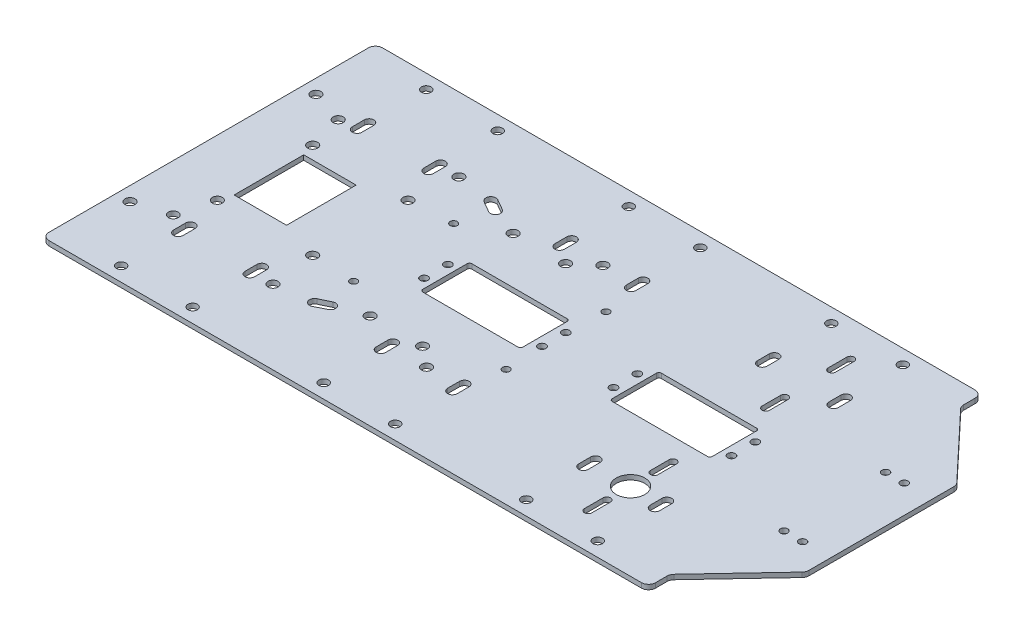
SolidWorks part; units mm, degrees
ref_plane "前视基准面" through (0, 0, 0) normal (0, 0, 1) x (1, 0, 0)
ref_plane "上视基准面" through (0, 0, 0) normal (0, 1, 0) x (1, 0, 0)
ref_plane "右视基准面" through (0, 0, 0) normal (1, 0, 0) x (0, 0, -1)
sketch "草图1" plane through (0, 0, 0) normal (0, 1, 0) x (1, 0, 0)
  line L0 (4082.7289, 1509.8503) -> (4060.7289, 1509.8503)
  line L1 (4175.7346, 1460.2503) -> (4175.7346, 1455.2395)
  line L2 (4145.7346, 1460.2503) -> (4145.7346, 1455.2395)
  line L3 (4179.7346, 1455.2395) -> (4179.7346, 1460.2503)
  line L4 (4115.6347, 1530.6257) -> (4120.1638, 1528.0129)
  line L5 (4060.7289, 1480.6503) -> (4082.7289, 1480.6503)
  line L6 (4094.7346, 1455.2395) -> (4094.7346, 1460.2503)
  line L7 (4149.7346, 1455.2395) -> (4149.7346, 1460.2503)
  line L8 (4122.2625, 1531.6509) -> (4117.7334, 1534.2637)
  line L9 (4060.7346, 1460.2503) -> (4060.7346, 1455.2395)
  line L10 (4234.7346, 1455.2395) -> (4234.7346, 1460.2503)
  line L11 (4064.7346, 1455.2395) -> (4064.7346, 1460.2503)
  line L12 (4090.7346, 1460.2503) -> (4090.7346, 1455.2395)
  line L13 (4060.7289, 1509.8503) -> (4060.7289, 1480.6503)
  line L14 (4082.7289, 1480.6503) -> (4082.7289, 1509.8503)
  line L15 (4090.7346, 1530.2503) -> (4090.7346, 1535.2611)
  line L16 (4176.5776, 1504.5503) -> (4176.5776, 1485.9503)
  line L17 (4175.5776, 1484.9503) -> (4135.5776, 1484.9503)
  line L18 (4094.7346, 1535.2611) -> (4094.7346, 1530.2503)
  line L19 (4115.7772, 1460.3388) -> (4120.3279, 1462.5177)
  line L20 (4149.7346, 1535.2611) -> (4149.7346, 1530.2503)
  line L21 (4060.7346, 1530.2503) -> (4060.7346, 1535.2611)
  line L22 (4145.7346, 1530.2503) -> (4145.7346, 1535.2611)
  line L23 (4122.1349, 1458.8376) -> (4117.6283, 1456.569)
  line L24 (4134.5776, 1485.9503) -> (4134.5776, 1504.5503)
  line L25 (4135.5776, 1505.5503) -> (4175.5776, 1505.5503)
  line L26 (4064.7346, 1535.2611) -> (4064.7346, 1530.2503)
  line L27 (4175.7346, 1530.2503) -> (4175.7346, 1535.2611)
  line L28 (4038.4346, 1425.2395) -> (4287.0345, 1425.2395)
  line L29 (4317.7347, 1464.8467) -> (4317.7347, 1525.6539)
  line L30 (4251.291, 1514.7632) -> (4251.291, 1522.5539)
  line L31 (4251.291, 1542.4908) -> (4251.291, 1550.2815)
  line L32 (4260.7346, 1460.2503) -> (4260.7346, 1455.2395)
  line L33 (4264.7346, 1455.2395) -> (4264.7346, 1460.2503)
  line L34 (4287.0345, 1565.2611) -> (4038.4346, 1565.2611)
  line L35 (4248.191, 1550.2815) -> (4248.191, 1542.4908)
  line L36 (4035.4346, 1562.2611) -> (4035.4346, 1428.2395)
  line L37 (4316.9188, 1527.7105) -> (4290.8504, 1555.3947)
  line L38 (4290.0345, 1557.4513) -> (4290.0345, 1562.2611)
  line L39 (4290.8504, 1435.106) -> (4316.9188, 1462.7901)
  line L40 (4248.191, 1522.5539) -> (4248.191, 1514.7632)
  line L41 (4230.7346, 1460.2503) -> (4230.7346, 1455.2395)
  line L42 (4290.0345, 1428.2395) -> (4290.0345, 1433.0493)
  line L43 (4256.0776, 1504.5503) -> (4256.0776, 1485.9503)
  line L44 (4230.7346, 1530.2503) -> (4230.7346, 1535.2611)
  line L45 (4260.7346, 1530.2503) -> (4260.7346, 1535.2611)
  line L46 (4255.0776, 1484.9503) -> (4215.0776, 1484.9503)
  line L47 (4215.0776, 1505.5503) -> (4255.0776, 1505.5503)
  line L48 (4179.7346, 1535.2611) -> (4179.7346, 1530.2503)
  line L49 (4248.191, 1467.9468) -> (4248.191, 1475.7374)
  line L50 (4234.7346, 1535.2611) -> (4234.7346, 1530.2503)
  line L51 (4214.0776, 1485.9503) -> (4214.0776, 1504.5503)
  line L52 (4248.191, 1440.2192) -> (4248.191, 1448.0098)
  line L53 (4251.291, 1475.7374) -> (4251.291, 1467.9468)
  line L54 (4264.7346, 1535.2611) -> (4264.7346, 1530.2503)
  line L55 (4251.291, 1448.0098) -> (4251.291, 1440.2192)
  arc A0 (4149.7346, 1460.2503) -> (4145.7346, 1460.2503) centre (4147.7346, 1460.2503) ccw
  arc A1 (4175.7346, 1455.2395) -> (4179.7346, 1455.2395) centre (4177.7346, 1455.2395) ccw
  arc A2 (4060.7346, 1455.2395) -> (4064.7346, 1455.2395) centre (4062.7346, 1455.2395) ccw
  circle A3 centre (4041.3063, 1456.3883) radius 2.1
  arc A4 (4064.7346, 1460.2503) -> (4060.7346, 1460.2503) centre (4062.7346, 1460.2503) ccw
  arc A5 (4179.7346, 1460.2503) -> (4175.7346, 1460.2503) centre (4177.7346, 1460.2503) ccw
  arc A6 (4090.7346, 1455.2395) -> (4094.7346, 1455.2395) centre (4092.7346, 1455.2395) ccw
  arc A7 (4230.7346, 1455.2395) -> (4234.7346, 1455.2395) centre (4232.7346, 1455.2395) ccw
  arc A8 (4117.7334, 1534.2637) -> (4115.6347, 1530.6257) centre (4116.6841, 1532.4447) ccw
  circle A9 centre (4055.2132, 1460.6687) radius 2.05
  arc A10 (4145.7346, 1455.2395) -> (4149.7346, 1455.2395) centre (4147.7346, 1455.2395) ccw
  circle A11 centre (4041.3063, 1534.3883) radius 2.1
  arc A12 (4094.7346, 1460.2503) -> (4090.7346, 1460.2503) centre (4092.7346, 1460.2503) ccw
  circle A13 centre (4055.2132, 1529.8319) radius 2.1
  circle A14 centre (4059.1243, 1515.2233) radius 2.1
  circle A15 centre (4059.1243, 1475.2233) radius 2.1
  arc A16 (4120.1638, 1528.0129) -> (4122.2625, 1531.6509) centre (4121.2132, 1529.8319) ccw
  arc A17 (4149.7346, 1535.2611) -> (4145.7346, 1535.2611) centre (4147.7346, 1535.2611) ccw
  arc A18 (4134.5776, 1485.9503) -> (4135.5776, 1484.9503) centre (4135.5776, 1485.9503) ccw
  arc A19 (4122.1349, 1458.8376) -> (4120.3279, 1462.5177) centre (4121.2132, 1460.6687) ccw
  arc A20 (4094.7346, 1535.2611) -> (4090.7346, 1535.2611) centre (4092.7346, 1535.2611) ccw
  arc A21 (4145.7346, 1530.2503) -> (4149.7346, 1530.2503) centre (4147.7346, 1530.2503) ccw
  arc A22 (4064.7346, 1535.2611) -> (4060.7346, 1535.2611) centre (4062.7346, 1535.2611) ccw
  circle A23 centre (4298.1991, 1473.9374) radius 1.55
  arc A24 (4060.7346, 1530.2503) -> (4064.7346, 1530.2503) centre (4062.7346, 1530.2503) ccw
  arc A25 (4175.5776, 1484.9503) -> (4176.5776, 1485.9503) centre (4175.5776, 1485.9503) ccw
  arc A26 (4115.7772, 1460.3388) -> (4117.6283, 1456.569) centre (4116.6841, 1458.4447) ccw
  circle A27 centre (4262.7346, 1559.2611) radius 2
  arc A28 (4090.7346, 1530.2503) -> (4094.7346, 1530.2503) centre (4092.7346, 1530.2503) ccw
  circle A29 centre (4306.0131, 1516.5632) radius 1.55
  circle A30 centre (4259.8276, 1500.2503) radius 1.6
  arc A31 (4176.5776, 1504.5503) -> (4175.5776, 1505.5503) centre (4175.5776, 1504.5503) ccw
  circle A32 centre (4298.1991, 1516.5632) radius 1.55
  circle A33 centre (4262.7346, 1431.2395) radius 2
  circle A34 centre (4306.0131, 1473.9374) radius 1.55
  arc A35 (4135.5776, 1505.5503) -> (4134.5776, 1504.5503) centre (4135.5776, 1504.5503) ccw
  arc A36 (4290.0345, 1562.2611) -> (4287.0345, 1565.2611) centre (4287.0345, 1562.2611) ccw
  arc A37 (4248.191, 1514.7632) -> (4251.291, 1514.7632) centre (4249.741, 1514.7632) ccw
  arc A38 (4038.4346, 1565.2611) -> (4035.4346, 1562.2611) centre (4038.4346, 1562.2611) ccw
  arc A39 (4264.7346, 1460.2503) -> (4260.7346, 1460.2503) centre (4262.7346, 1460.2503) ccw
  arc A40 (4317.7347, 1525.6539) -> (4316.9188, 1527.7105) centre (4314.7347, 1525.6539) ccw
  arc A41 (4234.7346, 1460.2503) -> (4230.7346, 1460.2503) centre (4232.7346, 1460.2503) ccw
  arc A42 (4248.191, 1542.4908) -> (4251.291, 1542.4908) centre (4249.741, 1542.4908) ccw
  arc A43 (4290.0345, 1557.4513) -> (4290.8504, 1555.3947) centre (4293.0345, 1557.4513) ccw
  arc A44 (4251.291, 1522.5539) -> (4248.191, 1522.5539) centre (4249.741, 1522.5539) ccw
  arc A45 (4035.4346, 1428.2395) -> (4038.4346, 1425.2395) centre (4038.4346, 1428.2395) ccw
  arc A46 (4251.291, 1550.2815) -> (4248.191, 1550.2815) centre (4249.741, 1550.2815) ccw
  arc A47 (4287.0345, 1425.2395) -> (4290.0345, 1428.2395) centre (4287.0345, 1428.2395) ccw
  arc A48 (4290.8504, 1435.106) -> (4290.0345, 1433.0493) centre (4293.0345, 1433.0493) ccw
  arc A49 (4316.9188, 1462.7901) -> (4317.7347, 1464.8467) centre (4314.7347, 1464.8467) ccw
  arc A50 (4260.7346, 1455.2395) -> (4264.7346, 1455.2395) centre (4262.7346, 1455.2395) ccw
  arc A51 (4234.7346, 1535.2611) -> (4230.7346, 1535.2611) centre (4232.7346, 1535.2611) ccw
  arc A52 (4214.0776, 1485.9503) -> (4215.0776, 1484.9503) centre (4215.0776, 1485.9503) ccw
  arc A53 (4260.7346, 1530.2503) -> (4264.7346, 1530.2503) centre (4262.7346, 1530.2503) ccw
  arc A54 (4230.7346, 1530.2503) -> (4234.7346, 1530.2503) centre (4232.7346, 1530.2503) ccw
  arc A55 (4255.0776, 1484.9503) -> (4256.0776, 1485.9503) centre (4255.0776, 1485.9503) ccw
  arc A56 (4179.7346, 1535.2611) -> (4175.7346, 1535.2611) centre (4177.7346, 1535.2611) ccw
  arc A57 (4215.0776, 1505.5503) -> (4214.0776, 1504.5503) centre (4215.0776, 1504.5503) ccw
  arc A58 (4256.0776, 1504.5503) -> (4255.0776, 1505.5503) centre (4255.0776, 1504.5503) ccw
  arc A59 (4251.291, 1475.7374) -> (4248.191, 1475.7374) centre (4249.741, 1475.7374) ccw
  arc A60 (4175.7346, 1530.2503) -> (4179.7346, 1530.2503) centre (4177.7346, 1530.2503) ccw
  arc A61 (4251.291, 1448.0098) -> (4248.191, 1448.0098) centre (4249.741, 1448.0098) ccw
  arc A62 (4264.7346, 1535.2611) -> (4260.7346, 1535.2611) centre (4262.7346, 1535.2611) ccw
  arc A63 (4248.191, 1467.9468) -> (4251.291, 1467.9468) centre (4249.741, 1467.9468) ccw
  arc A64 (4248.191, 1440.2192) -> (4251.291, 1440.2192) centre (4249.741, 1440.2192) ccw
  circle A65 centre (4147.7346, 1559.2611) radius 2
  circle A66 centre (4232.7346, 1559.2611) radius 2
  circle A67 centre (4210.3276, 1500.2503) radius 1.6
  circle A68 centre (4101.3063, 1456.3883) radius 2.1
  circle A69 centre (4163.6841, 1458.4447) radius 2.1
  circle A70 centre (4133.2132, 1525.2503) radius 2.1
  circle A71 centre (4163.6841, 1532.4447) radius 2.1
  circle A72 centre (4101.3063, 1534.3883) radius 2.1
  circle A73 centre (4177.7346, 1431.2395) radius 2
  circle A74 centre (4155.2132, 1525.2503) radius 2.1
  circle A75 centre (4155.2132, 1465.2503) radius 2.1
  circle A76 centre (4130.8276, 1490.2503) radius 1.6
  circle A77 centre (4117.1639, 1516.3492) radius 1.5
  circle A78 centre (4181.1639, 1474.3492) radius 1.5
  circle A79 centre (4133.2132, 1465.2503) radius 2.1
  circle A80 centre (4062.7346, 1559.2611) radius 2
  circle A81 centre (4180.3276, 1490.2503) radius 1.6
  circle A82 centre (4099.1243, 1515.2233) radius 2.1
  circle A83 centre (4099.1243, 1475.2233) radius 2.1
  circle A84 centre (4181.1639, 1516.2592) radius 1.5
  circle A85 centre (4259.8276, 1490.2503) radius 1.6
  circle A86 centre (4147.7346, 1431.2395) radius 2
  circle A87 centre (4177.7346, 1559.2611) radius 2
  circle A88 centre (4130.8276, 1500.2503) radius 1.6
  circle A89 centre (4210.3276, 1490.2503) radius 1.6
  circle A90 centre (4180.3276, 1500.2503) radius 1.6
  circle A91 centre (4092.7346, 1559.2611) radius 2
  circle A92 centre (4117.1639, 1474.3492) radius 1.5
  circle A93 centre (4249.741, 1457.9783) radius 6
  circle A94 centre (4232.7346, 1431.2395) radius 2
  circle A95 centre (4092.7346, 1431.2395) radius 2
  circle A96 centre (4062.7346, 1431.2395) radius 2
  dimension "D1" = 128.0216
extrude "凸台-拉伸1" add sketch "草图1" along normal blind 2
sketch "草图2" plane through (0, 2, 0) normal (0, 1, 0) x (1, 0, 0)
  circle A1 centre (4306.0131, 1473.9374) radius 1.55
  circle A2 centre (4298.1991, 1473.9374) radius 1.55
  circle A3 centre (4306.0131, 1516.5632) radius 1.55
  circle A4 centre (4262.7346, 1431.2395) radius 2 construction
  circle A5 centre (4262.7346, 1559.2611) radius 2 construction
  dimension "D1" = 42.6258
  dimension "D2" = 7.814
  dimension "D3" = 3.1
  dimension "D4" = 128.0216
